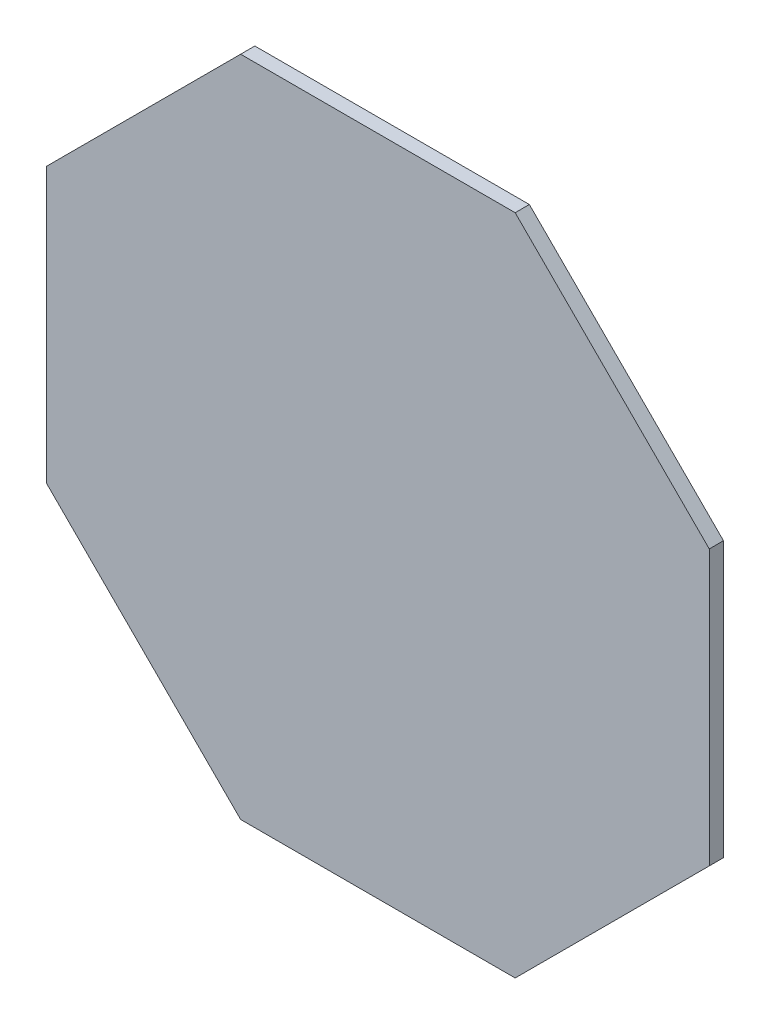
SolidWorks part; units mm, degrees
ref_plane "Front Plane" through (0, 0, 0) normal (0, 0, 1) x (1, 0, 0)
ref_plane "Top Plane" through (0, 0, 0) normal (0, 1, 0) x (1, 0, 0)
ref_plane "Right Plane" through (0, 0, 0) normal (1, 0, 0) x (0, 0, -1)
sketch "Sketch1" plane through (0, 0, 0) normal (0, 1, 0) x (1, 0, 0)
  line L0 (0, 0) -> (45.3198, 0) construction
  line L15 (0, 0) -> (38.2683, 15.8513) construction
  line L25 (35, 14.4975) -> (14.4975, 35)
  line L26 (14.4975, 35) -> (-14.4975, 35)
  line L27 (-14.4975, 35) -> (-35, 14.4975)
  line L28 (-35, 14.4975) -> (-35, -14.4975)
  line L29 (-35, -14.4975) -> (-14.4975, -35)
  line L30 (-14.4975, -35) -> (14.4975, -35)
  line L31 (14.4975, -35) -> (35, -14.4975)
  line L32 (35, -14.4975) -> (35, 14.4975)
  circle A0 centre (0, 0) radius 35 construction
  dimension "D1" = 35
sketch "Sketch2" plane through (0, 0, 0) normal (0, 0, 1) x (1, 0, 0)
  line L0 (0, 0) -> (35, 14.4975) construction
  line L1 (35, 14.4975) -> (14.4975, 35)
  line L2 (14.4975, 35) -> (-14.4975, 35)
  line L3 (-14.4975, 35) -> (-35, 14.4975)
  line L4 (-35, 14.4975) -> (-35, -14.4975)
  line L5 (-35, -14.4975) -> (-14.4975, -35)
  line L6 (-14.4975, -35) -> (14.4975, -35)
  line L7 (14.4975, -35) -> (35, -14.4975)
  line L8 (35, -14.4975) -> (35, 14.4975)
  circle A0 centre (0, 0) radius 35 construction
  dimension "D1" = 35
extrude "Boss-Extrude2" add sketch "Sketch2" along normal blind 1.5
